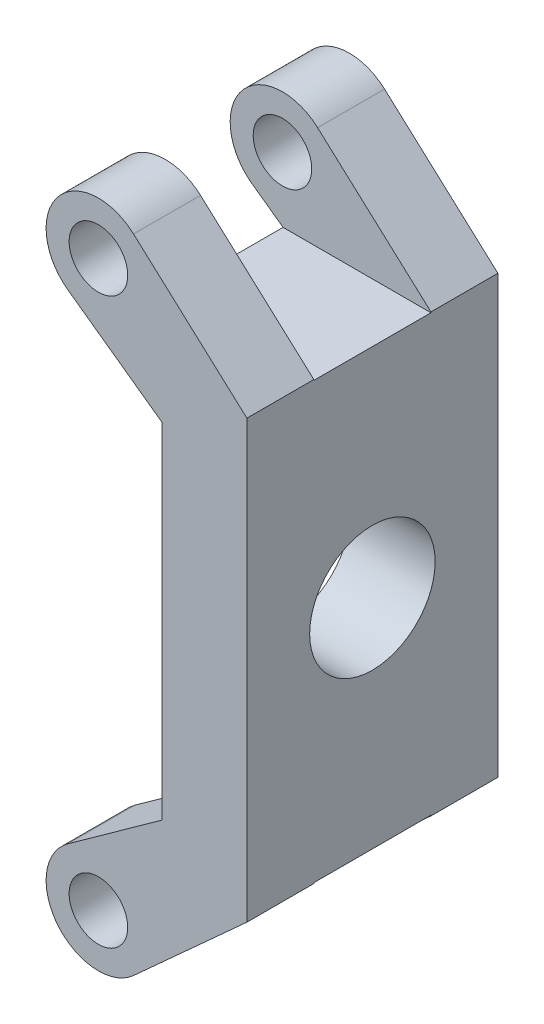
SolidWorks part; units mm, degrees
ref_plane "Front Plane" through (0, 0, 0) normal (0, 0, 1) x (1, 0, 0)
ref_plane "Top Plane" through (0, 0, 0) normal (0, 1, 0) x (1, 0, 0)
ref_plane "Right Plane" through (0, 0, 0) normal (1, 0, 0) x (0, 0, -1)
sketch "Sketch1" plane through (0, 0, 0) normal (1, 0, 0) x (0, 0, -1)
  line L0 (-7.5, 20) -> (-3.5, 20)
  line L1 (-7.5, 20) -> (7.5, 20) construction
  line L2 (-7.5, 20) -> (-7.5, -20)
  line L3 (-7.5, -20) -> (7.5, -20) construction
  line L4 (7.5, 20) -> (7.5, -20)
  line L5 (-7.5, 20) -> (7.5, -20) construction
  line L6 (-7.5, -20) -> (7.5, 20) construction
  line L7 (-3.5, 20) -> (-3.5, 13)
  line L8 (-3.5, 13) -> (3.5, 13)
  line L9 (3.5, 13) -> (3.5, 20)
  line L10 (3.5, -20) -> (3.5, -13)
  line L11 (3.5, -13) -> (-3.5, -13)
  line L12 (-3.5, -13) -> (-3.5, -20)
  line L13 (-3.5, -20) -> (-7.5, -20)
  line L14 (3.5, -20) -> (7.5, -20)
  line L15 (3.5, 20) -> (7.5, 20)
  circle A0 centre (0, 0) radius 3.75
  point P0 (0, 0)
  dimension "D4" = 7.5
  dimension "D1" = 7
  dimension "D2" = 7
  dimension "D3" = 40
  dimension "D5" = 4
extrude "Boss-Extrude1" add sketch "Sketch1" along normal blind 12
sketch "Sketch2" plane through (0, 0, 7.5) normal (0, 0, 1) x (1, 0, 0)
  line L0 (0, 16.874) -> (3.126, 16.874) construction
  line L1 (0, 20) -> (0, -20) construction
  line L2 (3.126, 16.874) -> (3.126, 20) construction
  line L3 (12, 20) -> (0, 20) construction
  line L4 (5.2264, 19.1892) -> (8.6132, 16.1164)
  line L5 (8.6132, 16.1164) -> (12, 13.0437)
  line L6 (12, 20) -> (12, -20) construction
  line L7 (12, 13.0437) -> (13.7413, 13.0437)
  line L8 (13.7413, 13.0437) -> (13.7413, 26.4469)
  line L9 (13.7413, 26.4469) -> (-3.729, 26.4469)
  line L10 (-3.729, 26.4469) -> (-3.729, -26.4469)
  line L11 (-3.729, -26.4469) -> (13.7413, -26.4469)
  line L12 (13.7413, -26.4469) -> (13.7413, -13.0437)
  line L13 (13.7413, -13.0437) -> (12, -13.0437)
  line L14 (12, -13.0437) -> (8.6132, -16.1164)
  line L15 (8.6132, -16.1164) -> (5.2264, -19.1892)
  line L16 (1.302, 14.3354) -> (6.9343, 10.2885)
  line L17 (6.9343, 10.2885) -> (6.9343, -10.2885)
  line L18 (6.9343, -10.2885) -> (1.302, -14.3354)
  line L19 (0, 0) -> (12, 0) construction
  line L20 (12, 13.0437) -> (12, -13.0437)
  line L21 (12, 13.0437) -> (12, -13.0437)
  line L22 (0, -16.874) -> (3.126, -16.874) construction
  line L23 (3.126, -16.874) -> (3.126, -20) construction
  line L24 (12, -20) -> (0, -20) construction
  circle A0 centre (3.126, 16.874) radius 1.75
  arc A1 (0, 16.874) -> (3.126, 20) centre (3.126, 16.874) cw
  arc A2 (0, 16.874) -> (1.302, 14.3354) centre (3.126, 16.874) ccw
  arc A3 (3.126, 20) -> (5.2264, 19.1892) centre (3.126, 16.874) cw
  arc A4 (5.2264, -19.1892) -> (1.302, -14.3354) centre (3.126, -16.874) cw
  circle A5 centre (3.126, -16.874) radius 1.75
  point P35 (6.9343, 0)
  line M1 (0, 20) -> (0, -20)
  line M2 (0, -20) -> (12, -20)
  line M3 (12, -20) -> (12, 20)
  line M4 (12, 20) -> (0, 20)
  dimension "D1" = 3.5
extrude "Cut-Extrude1" cut sketch "Sketch2" against normal through all contours A4 L18 L17 L16 A2 M1 | A1 M1 M4 | A0 | A3 L4 L5 M4 M3 | L15 A4 L14 M2 M3 | A4 M2 M1 | A5
